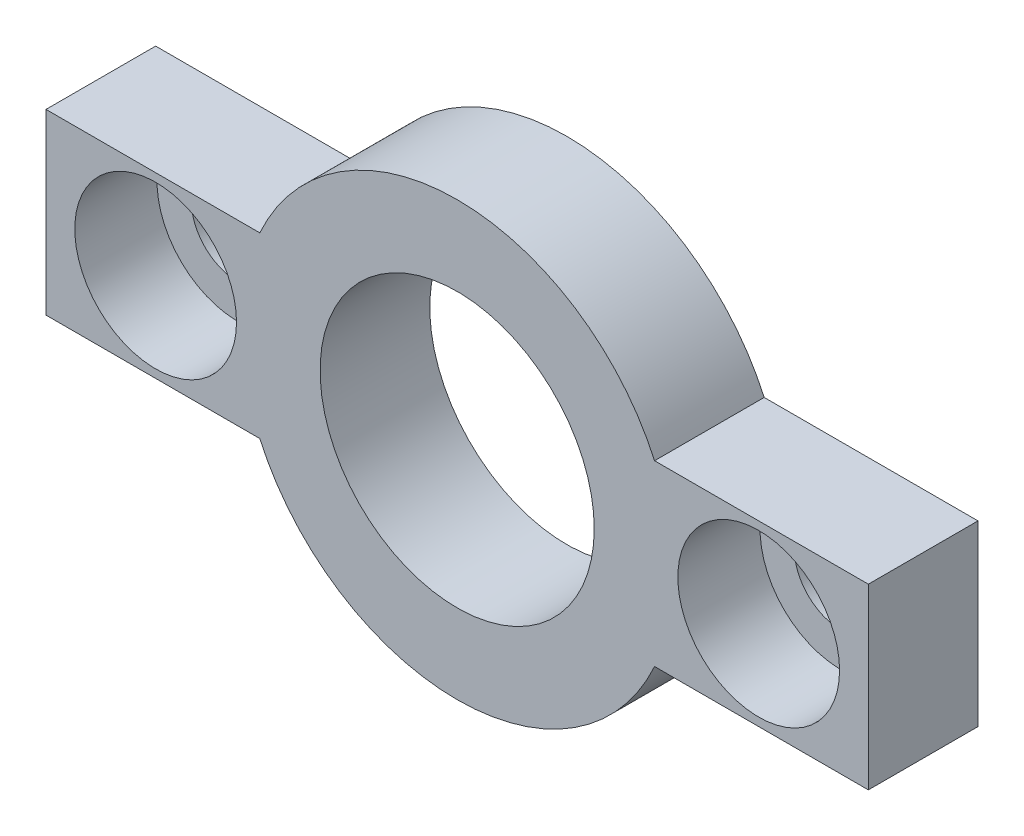
SolidWorks part; units mm, degrees
ref_plane "Alzado" through (0, 0, 0) normal (0, 0, 1) x (1, 0, 0)
ref_plane "Planta" through (0, 0, 0) normal (0, 1, 0) x (1, 0, 0)
ref_plane "Vista lateral" through (0, 0, 0) normal (1, 0, 0) x (0, 0, -1)
sketch "Croquis1" plane through (0, 0, 0) normal (0, 0, 1) x (1, 0, 0)
  line L0 (-7.2005, 3.25) -> (-15, 3.25)
  line L1 (15, -3.25) -> (7.2005, -3.25)
  line L2 (15, -3.25) -> (15, 3.25)
  line L3 (15, 3.25) -> (7.2005, 3.25)
  line L4 (-15, -3.25) -> (-15, 3.25)
  line L5 (15, -3.25) -> (-15, 3.25) construction
  line L6 (15, 3.25) -> (-15, -3.25) construction
  line L9 (-7.2005, -3.25) -> (-15, -3.25)
  arc A0 (-7.2005, -3.25) -> (7.2005, -3.25) centre (0, 0) ccw
  circle A1 centre (0, 0) radius 5
  arc A2 (7.2005, 3.25) -> (-7.2005, 3.25) centre (0, 0) ccw
  dimension "D3" = 10
  dimension "D4" = 7.9
  dimension "D1" = 30
  dimension "D2" = 6.5
extrude "Saliente-Extruir1" add sketch "Croquis1" along normal blind 4
sketch "Croquis2" plane through (0, 0, 4) normal (0, 0, 1) x (1, 0, 0)
  line L0 (-11, 0) -> (11, 0) construction
  circle A0 centre (-11, 0) radius 1.7
  circle A1 centre (11, 0) radius 1.7
  point P2 (0, 0)
  dimension "D1" = 3.4
  dimension "D2" = 22
extrude "Cortar-Extruir1" cut sketch "Croquis2" against normal blind 4
sketch "Croquis3" plane through (0, 0, 4) normal (0, 0, 1) x (1, 0, 0)
  circle A0 centre (-11, 0) radius 2.95
  circle A1 centre (11, 0) radius 2.95
  dimension "D1" = 5.9
extrude "Cortar-Extruir2" cut sketch "Croquis3" against normal blind 3
